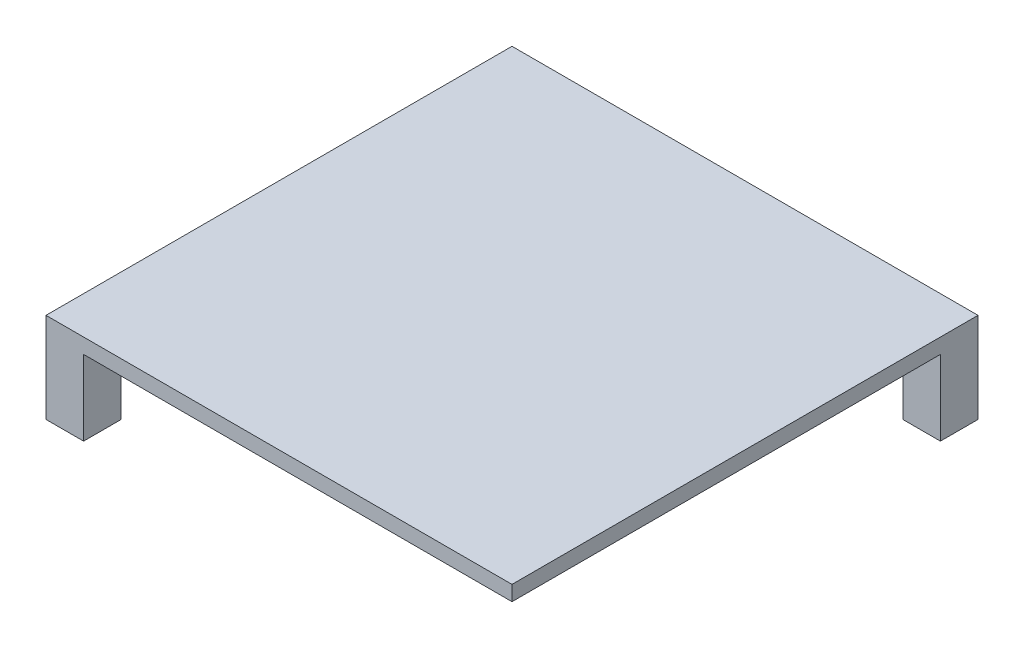
SolidWorks part; units mm, degrees
ref_plane "Front Plane" through (0, 0, 0) normal (0, 0, 1) x (1, 0, 0)
ref_plane "Top Plane" through (0, 0, 0) normal (0, 1, 0) x (1, 0, 0)
ref_plane "Right Plane" through (0, 0, 0) normal (1, 0, 0) x (0, 0, -1)
sketch "Sketch2" plane through (0, 0, 0) normal (0, 1, 0) x (1, 0, 0)
  line L1 (-31, -31) -> (31, -31)
  line L2 (-31, -31) -> (-31, 31)
  line L3 (-31, 31) -> (31, 31)
  line L4 (31, -31) -> (31, 31)
  line L5 (-31, -31) -> (31, 31) construction
  line L6 (-31, 31) -> (31, -31) construction
  point P0 (0, 0)
  dimension "D1" = 62
extrude "Boss-Extrude1" add sketch "Sketch2" along normal blind 2
sketch "Sketch3" plane through (0, 0, 0) normal (0, -1, 0) x (1, 0, 0)
  line L1 (-31, 31) -> (-26, 31)
  line L2 (-31, 31) -> (-31, 26)
  line L3 (-31, 26) -> (-26, 26)
  line L4 (-26, 31) -> (-26, 26)
  line L6 (-31, 31) -> (31, 31) construction
  line L7 (-31, -31) -> (-31, 31) construction
  dimension "D1" = 5
extrude "Boss-Extrude2" add sketch "Sketch3" along normal blind 10
sketch "Sketch6" plane through (0, -10, 0) normal (0, -1, 0) x (1, 0, 0)
  line L0 (-31, 31) -> (-26, 26) construction
  line L1 (-31, 26) -> (-26, 31) construction
  circle A0 centre (-28.5, 28.5) radius 1
  point P8 (-28.5, 28.5)
  dimension "D1" = 2
extrude "Cut-Extrude2" cut sketch "Sketch6" against normal blind 3
sketch "Sketch7" plane through (0, 0, 0) normal (0, 0, 1) x (1, 0, 0)
  line L0 (0, 0) -> (0, 2) construction
  line L1 (-31, 2) -> (31, 2) construction
pattern_circular "CirPattern1" count 3 every 90 about axis through (0, 0, 0) along (0, 1, 0) of "Cut-Extrude2", "Boss-Extrude2"
